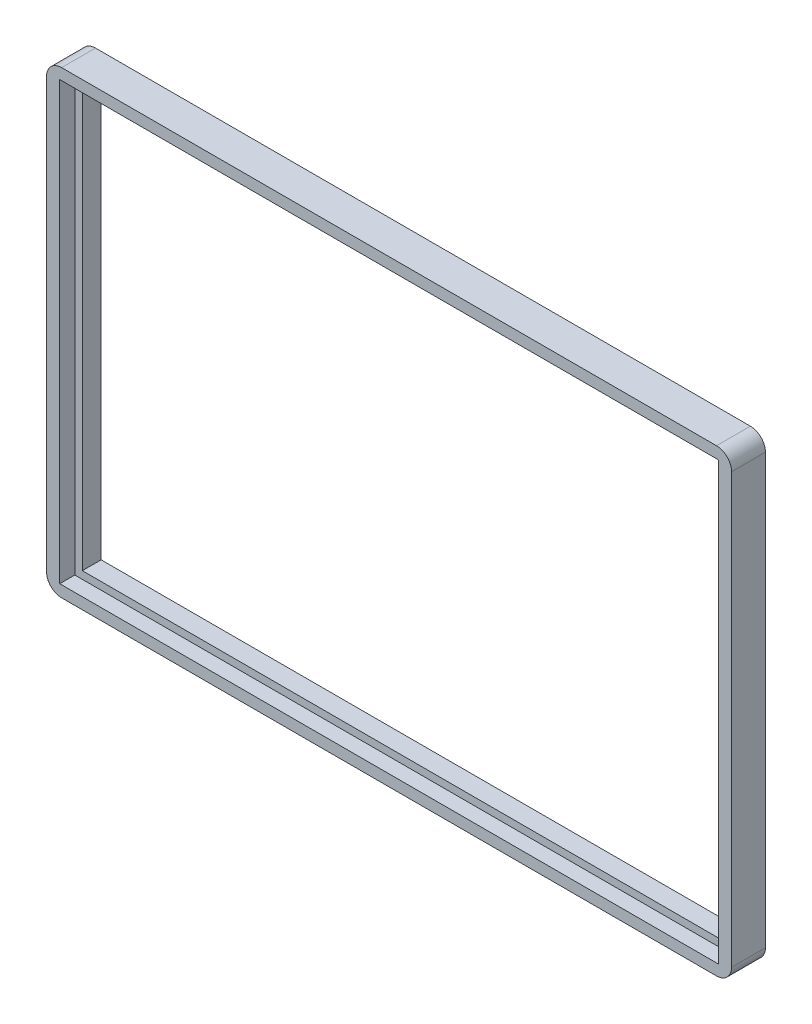
SolidWorks part; units mm, degrees
ref_plane "Front Plane" through (0, 0, 0) normal (0, 0, 1) x (1, 0, 0)
ref_plane "Top Plane" through (0, 0, 0) normal (0, 1, 0) x (1, 0, 0)
ref_plane "Right Plane" through (0, 0, 0) normal (1, 0, 0) x (0, 0, -1)
sketch "Sketch1" plane through (0, 0, 0) normal (0, 0, 1) x (1, 0, 0)
  line L1 (-45.5, 30.5) -> (45.5, 30.5)
  line L2 (-45.5, 30.5) -> (-45.5, -30.5)
  line L3 (-45.5, -30.5) -> (45.5, -30.5)
  line L4 (45.5, 30.5) -> (45.5, -30.5)
  line L5 (-45.5, 30.5) -> (45.5, -30.5) construction
  line L6 (-45.5, -30.5) -> (45.5, 30.5) construction
  point P0 (0, 0)
  dimension "D1" = 91
  dimension "D2" = 61
extrude "Boss-Extrude1" add sketch "Sketch1" along normal blind 4.5
sketch "Sketch2" plane through (0, 0, 4.5) normal (0, 0, 1) x (1, 0, 0)
  line L1 (-43.75, 29) -> (43.75, 29)
  line L2 (-43.75, 29) -> (-43.75, -29)
  line L3 (-43.75, -29) -> (43.75, -29)
  line L4 (43.75, 29) -> (43.75, -29)
  line L5 (-43.75, 29) -> (43.75, -29) construction
  line L6 (-43.75, -29) -> (43.75, 29) construction
  point P0 (0, 0)
  dimension "D1" = 87.5
  dimension "D2" = 58
extrude "Cut-Extrude1" cut sketch "Sketch2" against normal blind 2
sketch "Sketch3" plane through (0, 0, 2.5) normal (0, 0, 1) x (1, 0, 0)
  line L0 (-43.75, 29) -> (-43.75, -29) construction
  line L1 (-42.75, 28) -> (42.75, 28)
  line L2 (-42.75, 28) -> (-42.75, -28)
  line L3 (-42.75, -28) -> (42.75, -28)
  line L4 (42.75, 28) -> (42.75, -28)
  line L5 (-42.75, 28) -> (42.75, -28) construction
  line L6 (-42.75, -28) -> (42.75, 28) construction
  line L7 (43.75, 29) -> (-43.75, 29) construction
  point P0 (0, 0)
  dimension "D1" = 1
  dimension "D2" = 1
extrude "Cut-Extrude2" cut sketch "Sketch3" against normal through all
fillet "Fillet1" radius 2 4 edges at (45.5, 30.5, 2.25) (45.5, -30.5, 2.25) (-45.5, -30.5, 2.25) (-45.5, 30.5, 2.25)
sketch "Sketch5" plane through (0, -30.5, 0) normal (0, -1, 0) x (1, 0, 0)
  line L0 (0, 4.5) -> (35.5, 4.5)
  line L1 (-43.5, 4.5) -> (43.5, 4.5) construction
  line L2 (35.5, 4.5) -> (35.5, 2.5)
  line L3 (35.5, 2.5) -> (-35.5, 2.5)
  line L4 (-35.5, 2.5) -> (-35.5, 4.5)
  line L5 (-35.5, 4.5) -> (0, 4.5)
  line L6 (-43.75, 2.5) -> (43.75, 2.5) construction
  line L7 (45.5, 4.5) -> (45.5, 0) construction
  line L8 (-45.5, 0) -> (-45.5, 4.5) construction
  dimension "D1" = 10
  dimension "D2" = 10
equation "\"D2@Sketch5\"=\"D1@Sketch5\""
